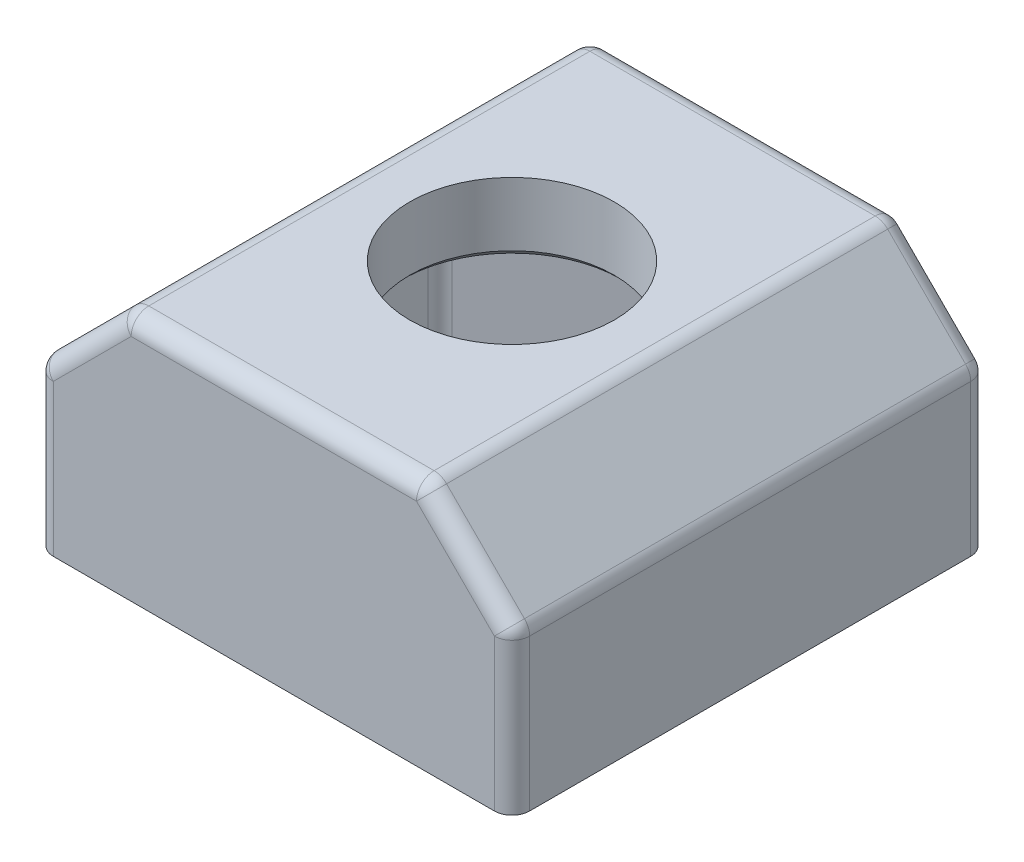
SolidWorks part; units mm, degrees
ref_plane "Front Plane" through (0, 0, 0) normal (0, 0, 1) x (1, 0, 0)
ref_plane "Top Plane" through (0, 0, 0) normal (0, 1, 0) x (1, 0, 0)
ref_plane "Right Plane" through (0, 0, 0) normal (1, 0, 0) x (0, 0, -1)
sketch "Sketch1" plane through (0, 0, 0) normal (0, 1, 0) x (1, 0, 0)
  line L1 (0, -5.7158) -> (4.95, -2.8579)
  line L2 (4.95, -2.8579) -> (4.95, 2.8579)
  line L3 (4.95, 2.8579) -> (0, 5.7158)
  line L4 (0, 5.7158) -> (-4.95, 2.8579)
  line L5 (-4.95, 2.8579) -> (-4.95, -2.8579)
  line L6 (-4.95, -2.8579) -> (0, -5.7158)
  line L7 (-6.75, 6.75) -> (6.75, 6.75)
  line L8 (-6.75, 6.75) -> (-6.75, -6.75)
  line L9 (-6.75, -6.75) -> (6.75, -6.75)
  line L10 (6.75, 6.75) -> (6.75, -6.75)
  line L11 (-6.75, 6.75) -> (6.75, -6.75) construction
  line L12 (-6.75, -6.75) -> (6.75, 6.75) construction
  circle A0 centre (0, 0) radius 4.95 construction
  dimension "D1" = 9.9
  dimension "D2" = 13.5
extrude "Boss-Extrude1" add sketch "Sketch1" along normal blind 5
sketch "Sketch3" plane through (0, 5, 0) normal (0, 1, 0) x (1, 0, 0)
  line L4 (6.75, 6.75) -> (-6.75, 6.75)
  line L5 (-6.75, 6.75) -> (-6.75, -6.75)
  line L6 (-6.75, -6.75) -> (6.75, -6.75)
  line L7 (6.75, -6.75) -> (6.75, 6.75)
  line L8 (6.75, 6.75) -> (-6.75, 6.75)
  line L9 (-6.75, 6.75) -> (-6.75, -6.75)
  line L10 (-6.75, -6.75) -> (6.75, -6.75)
  line L11 (6.75, -6.75) -> (6.75, 6.75)
  dimension "D1" = 0
extrude "Boss-Extrude2" add sketch "Sketch3" along normal blind 2
chamfer "Chamfer1" distance 2.5 angle 45 2 edges at (6.75, 7, 0) (-6.75, 7, 0)
fillet "Fillet2" radius 0.5 6 edges at (-4.95, 2.5, -2.8579) (-4.95, 2.5, 2.8579) (0, 2.5, 5.7158) (4.95, 2.5, 2.8579) (4.95, 2.5, -2.8579) (0, 2.5, -5.7158)
fillet "Fillet1" radius 0.5 14 edges at (-6.75, 2.25, -6.75) (-6.75, 2.25, 6.75) (6.75, 2.25, -6.75) (6.75, 2.25, 6.75) (-5.5, 5.75, -6.75) (0, 7, -6.75) (5.5, 5.75, -6.75) (5.5, 5.75, 6.75) (0, 7, 6.75) (-5.5, 5.75, 6.75) (6.75, 4.5, 0) (4.25, 7, 0) (-4.25, 7, 0) (-6.75, 4.5, 0)
sketch "Sketch4" plane through (0, 5, 0) normal (0, -1, 0) x (1, 0, 0)
  circle A0 centre (0, 0) radius 2.9
  dimension "D1" = 5.8
extrude "Cut-Extrude1" cut sketch "Sketch4" against normal up to next
chamfer "Chamfer2" distance 0.2 angle 45 1 edges at (0, 5, -2.9)
